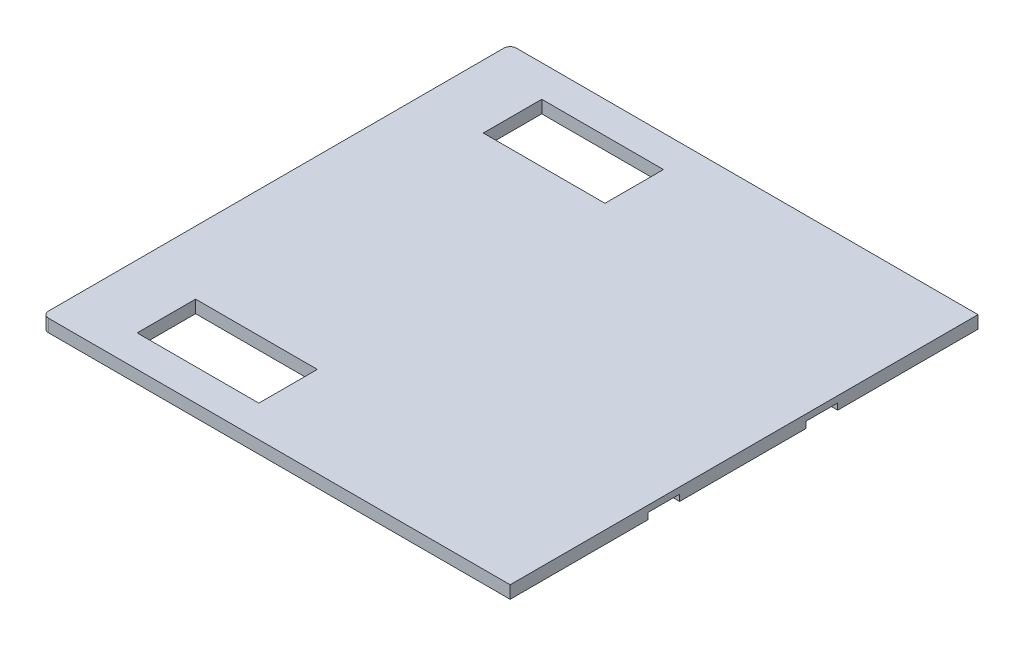
SolidWorks part; units mm, degrees
ref_plane "Plan de face" through (0, 0, 0) normal (0, 0, 1) x (1, 0, 0)
ref_plane "Plan de dessus" through (0, 0, 0) normal (0, 1, 0) x (1, 0, 0)
ref_plane "Plan de droite" through (0, 0, 0) normal (1, 0, 0) x (0, 0, -1)
sketch "Esquisse1" plane through (0, 0, 0) normal (0, 1, 0) x (1, 0, 0)
  line L1 (-74, 74) -> (74, 74)
  line L2 (-74, 74) -> (-74, -74)
  line L3 (-74, -74) -> (74, -74)
  line L4 (74, 74) -> (74, -74)
  line L5 (-74, 74) -> (74, -74) construction
  line L6 (-74, -74) -> (74, 74) construction
  point P0 (0, 0)
extrude "Boss.-Extru.1" add sketch "Esquisse1" along normal blind 4
fillet "Congé1" radius 2 2 edges at (-74, 2, -74) (-74, 2, 74)
sketch "Esquisse12" plane through (0, 0, 0) normal (0, 1, 0) x (1, 0, 0)
  line L0 (80.5612, -25.3842) -> (80.5612, -20.3842) construction
  line L1 (74.0521, 24.6158) -> (74.0521, 29.6158) construction
  line L2 (80.5612, -25.3842) -> (56.9202, -25.3842) construction
  line L3 (80.5612, -25.3842) -> (80.5612, -30.3842) construction
  line L4 (74.0521, 24.6158) -> (56.9202, 24.6158) construction
  line L5 (80.5612, -20.3842) -> (56.9202, -20.3842)
  line L6 (80.5612, -20.3842) -> (80.5612, -30.3842)
  line L7 (80.5612, -30.3842) -> (56.9202, -30.3842)
  line L8 (56.9202, -20.3842) -> (56.9202, -30.3842)
  line L9 (74.0521, 24.6158) -> (74.0521, 19.6158) construction
  line L11 (74.0521, 29.6158) -> (56.9202, 29.6158)
  line L12 (74.0521, 29.6158) -> (74.0521, 19.6158)
  line L13 (74.0521, 19.6158) -> (56.9202, 19.6158)
  line L14 (56.9202, 29.6158) -> (56.9202, 19.6158)
  point P12 (80.5612, -25.3842)
extrude "Enlèv. mat.-Extru.12" cut sketch "Esquisse12" along normal blind 2
sketch "Esquisse13" plane through (0, 0, 0) normal (0, 1, 0) x (1, 0, 0)
  line L0 (-54, -74) -> (-54, -64) construction
  line L1 (-72, -74) -> (74, -74) construction
  line L2 (-54, -64) -> (-74, -64) construction
  line L3 (-74, 72) -> (-74, -72) construction
  line L4 (-54, 74) -> (-54, 64) construction
  line L5 (-54, -64) -> (-15.5, -64)
  line L6 (-54, -64) -> (-54, -45.5)
  line L7 (-54, -45.5) -> (-15.5, -45.5)
  line L8 (-15.5, -64) -> (-15.5, -45.5)
  line L9 (74, 74) -> (-72, 74) construction
  line L10 (-54, 64) -> (-74, 64) construction
  line L12 (-54, 64) -> (-15.5, 64)
  line L13 (-54, 64) -> (-54, 45.5)
  line L14 (-54, 45.5) -> (-15.5, 45.5)
  line L15 (-15.5, 64) -> (-15.5, 45.5)
extrude "Enlèv. mat.-Extru.13" cut sketch "Esquisse13" along normal blind 5
